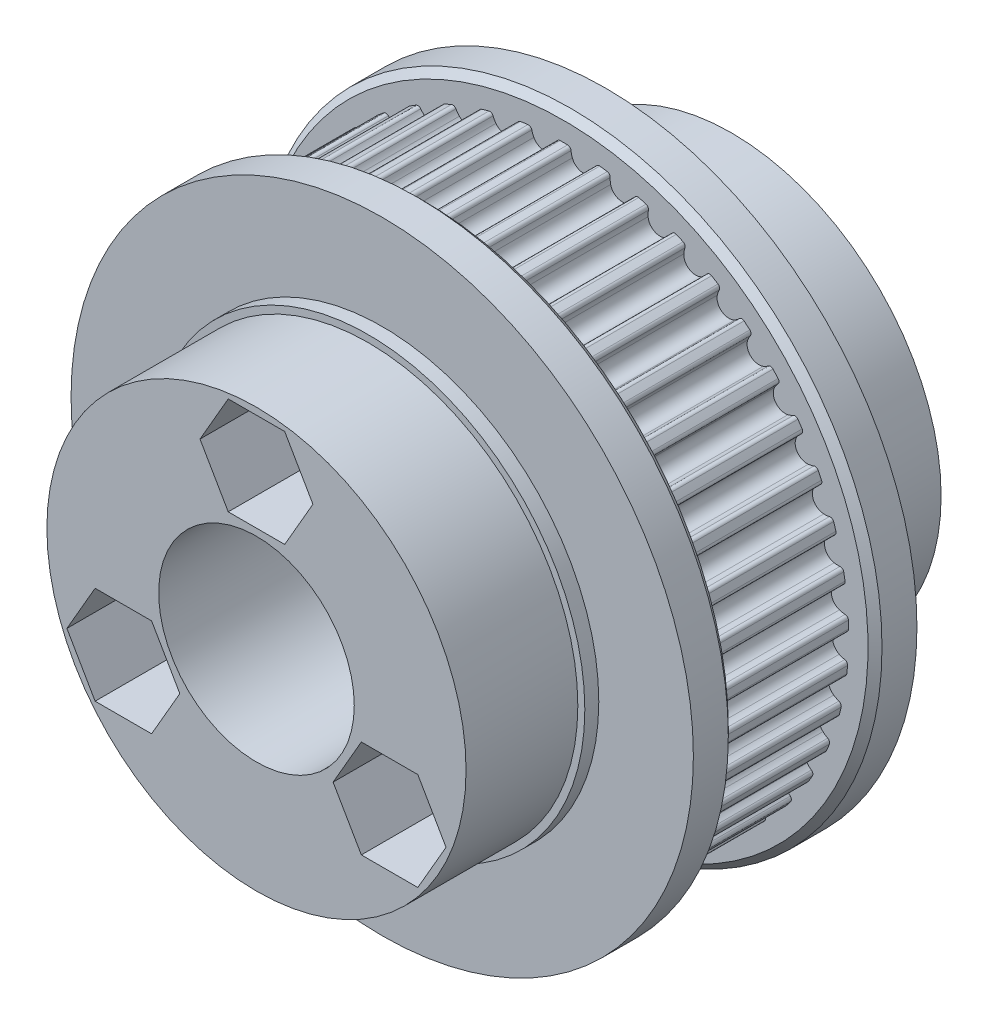
SolidWorks part; units mm, degrees
material "ABS"
ref_plane "正面" through (0, 0, 0) normal (0, 0, 1) x (1, 0, 0)
ref_plane "平面" through (0, 0, 0) normal (0, 1, 0) x (1, 0, 0)
ref_plane "右側面" through (0, 0, 0) normal (1, 0, 0) x (0, 0, -1)
sketch "ｽｹｯﾁ1" plane through (0, 0, 0) normal (0, 0, 1) x (1, 0, 0)
  circle A0 centre (0, 0) radius 20.7697
  dimension "D1" = 41.5394
extrude "ﾎﾞｽ - 押し出し1" add sketch "ｽｹｯﾁ1" along normal mid plane 10
sketch "ｽｹｯﾁ2" plane through (0, 0, 5) normal (0, 0, 1) x (1, 0, 0)
  line L0 (0, 20.3887) -> (0, 0) construction
  line L1 (0, 0) -> (1.402, 20.0498) construction
  line L2 (0, 20.7697) -> (0, 20.3887)
  line L3 (1.3427, 19.2018) -> (1.4488, 20.7191)
  arc A0 (0, 20.3887) -> (0.2693, 20.3869) centre (0, 0) cw
  arc A1 (0.5151, 20.1577) -> (0.6055, 19.753) centre (2.0299, 20.2837) ccw
  arc A2 (0.5151, 20.1577) -> (0.2693, 20.3869) centre (0.266, 20.137) ccw
  arc A3 (1.3427, 19.2018) -> (0.6055, 19.753) centre (1.402, 20.0498) cw
  circle A4 centre (0, 0) radius 20.7697 construction
  circle A5 centre (0, 0) radius 20.7697 construction
  circle A6 centre (0, 0) radius 19.2487 construction
  circle A7 centre (0, 0) radius 20.3887 construction
  arc A8 (0, 20.7697) -> (1.4488, 20.7191) centre (0, 0) cw
  circle M4 centre (0, 0) radius 20.7697
  dimension "D1" = 0.25
  dimension "D2" = 1.52
  dimension "D3" = 0.85
  dimension "D4" = 0.61
  dimension "D5" = 0.381
  dimension "D6" = 4
  dimension "D7" = 1.14
extrude "ｶｯﾄ - 押し出し1" cut sketch "ｽｹｯﾁ2" against normal through all contours A3 L3 L2 A0 A2 A1 M4
mirror "ﾐﾗｰ1" about plane through (0, 0, 0) normal (1, 0, 0) of "ｶｯﾄ - 押し出し1"
pattern_circular "円形ﾊﾟﾀｰﾝ1" count 45 over 360 about axis through (0, 0, 0) along (0, 0, 1) of "ﾐﾗｰ1", "ｶｯﾄ - 押し出し1"
sketch "ｽｹｯﾁ3" plane through (0, 0, 5) normal (0, 0, 1) x (1, 0, 0)
  circle A0 centre (0, 0) radius 22.2697
  dimension "D1" = 44.5394
extrude "ﾎﾞｽ - 押し出し2" add sketch "ｽｹｯﾁ3" along normal blind 3
chamfer "面取り1" distance 0.5 angle 45 1 edges at (22.2697, 0, 5)
sketch "ｽｹｯﾁ7" plane through (0, 0, -5) normal (0, 0, -1) x (-1, 0, 0)
  circle A0 centre (0, 0) radius 22.2697
  circle A1 centre (0, 0) radius 22.2697 construction
extrude "ﾎﾞｽ - 押し出し3" add sketch "ｽｹｯﾁ7" along normal blind 3 contours A0
chamfer "面取り2" distance 0.5 angle 45 1 edges at (-22.2697, 0, -5)
sketch "ｽｹｯﾁ8" plane through (0, 0, -8) normal (0, 0, -1) x (-1, 0, 0)
  circle A0 centre (0, 0) radius 15.5
  dimension "D1" = 31
extrude "ﾎﾞｽ - 押し出し4" add sketch "ｽｹｯﾁ8" along normal blind 1
sketch "ｽｹｯﾁ9" plane through (0, 0, -9) normal (0, 0, -1) x (-1, 0, 0)
  circle A0 centre (0, 0) radius 15
  dimension "D1" = 30
extrude "ﾎﾞｽ - 押し出し5" add sketch "ｽｹｯﾁ9" along normal blind 8
mirror "ﾐﾗｰ2" about plane through (0, 0, 0) normal (0, 0, 1) of "ﾎﾞｽ - 押し出し5", "ﾎﾞｽ - 押し出し4"
sketch "ｽｹｯﾁ4" plane through (0, 0, 0) normal (0, 0, 1) x (1, 0, 0)
  circle A0 centre (0, 0) radius 7
  dimension "D1" = 14
extrude "ｶｯﾄ - 押し出し2" cut sketch "ｽｹｯﾁ4" against normal through all both and the other way through all
hole_wizard "M4 すきま穴1" positions "ｽｹｯﾁ11" profile "ｽｹｯﾁ12" hole size "M4" standard "JIS" end condition through all
sketch "ｽｹｯﾁ11" plane through (0, 0, -17) normal (0, 0, -1) x (-1, 0, 0)
  point P0 (0, 11)
  dimension "D1" = 11
sketch "ｽｹｯﾁ12" plane through (0, 11, -17) normal (1, 0, 0) x (0, 1, 0)
  line L0 (0, 0) -> (0, 34)
  line L1 (0, 34) -> (2.4, 34)
  line L2 (2.4, 34) -> (2.4, 0)
  line L5 (2.4, 0) -> (0, 0)
  line L11 (0, -6.35) -> (0, 107.95) construction
  dimension "通し穴の直径" = 4.8
  dimension "通し穴の深さ" = 34
sketch "ｽｹｯﾁ13" plane through (0, 0, 17) normal (0, 0, 1) x (1, 0, 0)
  line L1 (-2.0207, 7.5) -> (2.0207, 7.5)
  line L2 (2.0207, 7.5) -> (4.0415, 11)
  line L3 (4.0415, 11) -> (2.0207, 14.5)
  line L4 (2.0207, 14.5) -> (-2.0207, 14.5)
  line L5 (-2.0207, 14.5) -> (-4.0415, 11)
  line L6 (-4.0415, 11) -> (-2.0207, 7.5)
  circle A0 centre (0, 11) radius 3.5 construction
  dimension "D1" = 7
extrude "ｶｯﾄ - 押し出し4" cut sketch "ｽｹｯﾁ13" against normal blind 6.4
sketch "ｽｹｯﾁ14" plane through (0, 0, 17) normal (0, 0, 1) x (1, 0, 0)
  circle A0 centre (-2.0207, 14.5) radius 0.5
  dimension "D1" = 1
extrude "ｶｯﾄ - 押し出し5" [suppressed] cut sketch "ｽｹｯﾁ14" against normal blind 2.6
pattern_circular "円形ﾊﾟﾀｰﾝ2" [suppressed] count 6 over 360
pattern_circular "円形ﾊﾟﾀｰﾝ3" count 3 over 360 about axis through (0, 0, 0) along (0, 0, 1) of "円形ﾊﾟﾀｰﾝ2", "M4 すきま穴1", "ｶｯﾄ - 押し出し4"
equation "\"n\"= 45"
equation "\"p\"= 2.9"
equation "\"pd\"= \"n\" * \"p\" / pi"
equation "\"D1@ｽｹｯﾁ1\"=\"pd\""
equation "\"width\"= 10mm"
equation "\"D1@ﾎﾞｽ - 押し出し1\"=\"width\""
equation "\"r1\"= 0.25mm"
equation "\"r2\"= 1.52mm"
equation "\"r3\"= 0.85mm"
equation "\"b\"= 0.61mm"
equation "\"h2\"= 1.14mm"
equation "\"h1\"= 2.4mm"
equation "\"i\"= 1.26mm"
equation "\"pld\"= 0.381mm"
equation "\"D1@ｽｹｯﾁ2\"=\"r1\""
equation "\"D2@ｽｹｯﾁ2\"=\"r2\""
equation "\"D3@ｽｹｯﾁ2\"=\"r3\""
equation "\"D4@ｽｹｯﾁ2\"=\"b\""
equation "\"D5@ｽｹｯﾁ2\"=\"pld\""
equation "\"angle\"= 180 / \"n\""
equation "\"D6@ｽｹｯﾁ2\"=\"angle\""
equation "\"D7@ｽｹｯﾁ2\"=\"h2\""
equation "\"D1@円形ﾊﾟﾀｰﾝ1\"=\"n\""
equation "\"D1@ｽｹｯﾁ3\"=\"pd\"+3"
